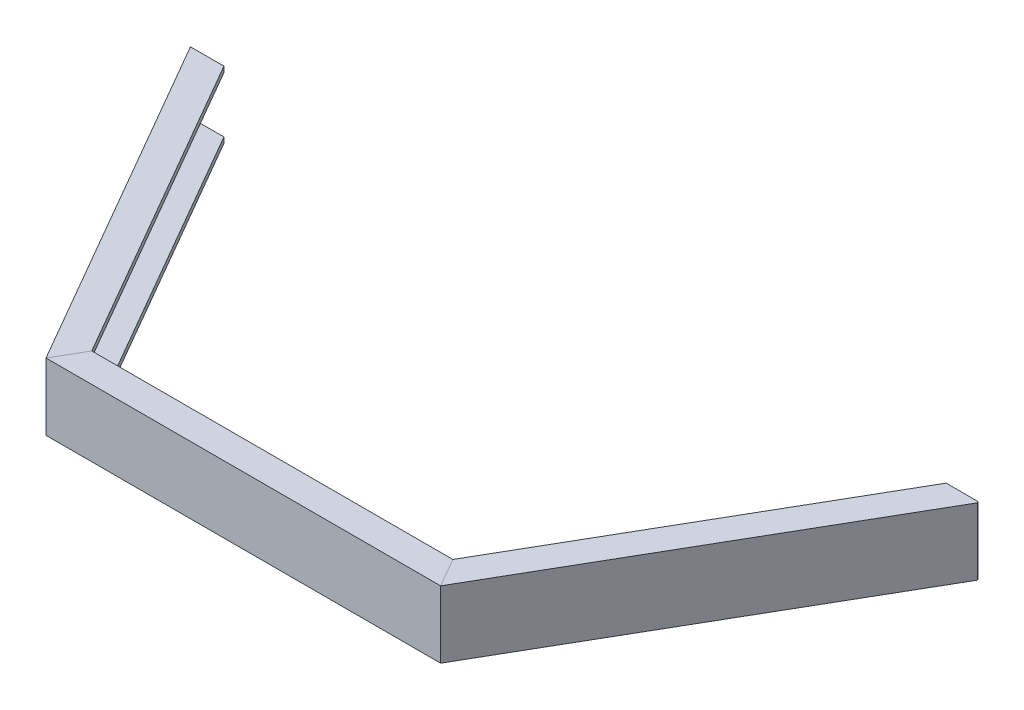
SolidWorks part; units mm, degrees
material "1.0035 (S185)"
ref_plane "Front Plane" through (0, 0, 0) normal (0, 0, 1) x (1, 0, 0)
ref_plane "Top Plane" through (0, 0, 0) normal (0, 1, 0) x (1, 0, 0)
ref_plane "Right Plane" through (0, 0, 0) normal (1, 0, 0) x (0, 0, -1)
sketch3d "3DSketch4"
  line L0 (-586.5879, 0, 0) -> (-293.2939, 0.0003, 508)
  line L1 (-293.2939, 0.0003, 508) -> (293.2939, -0.0003, 508)
  line L4 (293.2939, -0.0003, 508) -> (586.5879, 0, 0)
  circle A0 centre (0, 0, 0) radius 381 construction
  point P4 (0, 0, 0)
  point P5 (-439.9409, 0.0001, 254)
  point P8 (0, 381, 0)
  point P9 (0, 0, 0)
  point P10 (439.9409, -0.0001, 254)
  point P11 (0, 0, 0)
  point P12 (0, 0, 508)
  dimension "D3" = 508
  dimension "D4" = 762
  dimension "D1" = 508
  dimension "D5" = 120
  dimension "D6" = 120
  dimension "D2" = 508
sketch "Sketch1" plane through (0, 0, 0) normal (0, 0, 1) x (1, 0, 0)
  line L0 (-539.0879, 49.2015) -> (-589.0879, 49.2015)
  line L1 (-589.0879, 49.2015) -> (-589.0879, -50.7985)
  line L2 (-589.0879, -50.7985) -> (-539.0879, -50.7985)
  line L3 (-539.0879, -50.7985) -> (-539.0879, -42.2985)
  line L4 (-539.0879, -42.2985) -> (-575.0879, -42.2985)
  line L5 (-584.0879, -33.2985) -> (-584.0879, 31.7015)
  line L6 (-575.0879, 40.7015) -> (-539.0879, 40.7015)
  line L7 (-539.0879, 40.7015) -> (-539.0879, 49.2015)
  arc A0 (-575.0879, -42.2985) -> (-584.0879, -33.2985) centre (-575.0879, -33.2985) cw
  arc A1 (-584.0879, 31.7015) -> (-575.0879, 40.7015) centre (-575.0879, 31.7015) cw
  dimension "D7" = 9
  dimension "D1" = 50
  dimension "D2" = 100
  dimension "D3" = 5
  dimension "D4" = 8.5
  dimension "D5" = 8.5
  dimension "D6" = 2.5
sweep "Sweep1" add profiles "Sketch1" path "3DSketch4"
sketch "Sketch2" plane through (0, 0, 0) normal (0, 0, 1) x (1, 0, 0)
  line L1 (-1550.7116, -207.8474) -> (1550.7116, -207.8474)
  line L2 (-1550.7116, -207.8474) -> (-1550.7116, 207.8474)
  line L3 (-1550.7116, 207.8474) -> (1550.7116, 207.8474)
  line L4 (1550.7116, -207.8474) -> (1550.7116, 207.8474)
  line L5 (-1550.7116, -207.8474) -> (1550.7116, 207.8474) construction
  line L6 (-1550.7116, 207.8474) -> (1550.7116, -207.8474) construction
  point P0 (0, 0)
extrude "Cut-Extrude1" cut sketch "Sketch2" against normal through all
equation "\"D5@Sketch1\"=\"D4@Sketch1\""
equation "\"D6@Sketch1\"=\"D3@Sketch1\"/2"
equation "\"D3@3DSketch4\"=\"D2@3DSketch4\""
equation "\"D1@3DSketch4\"=\"D2@3DSketch4\""
